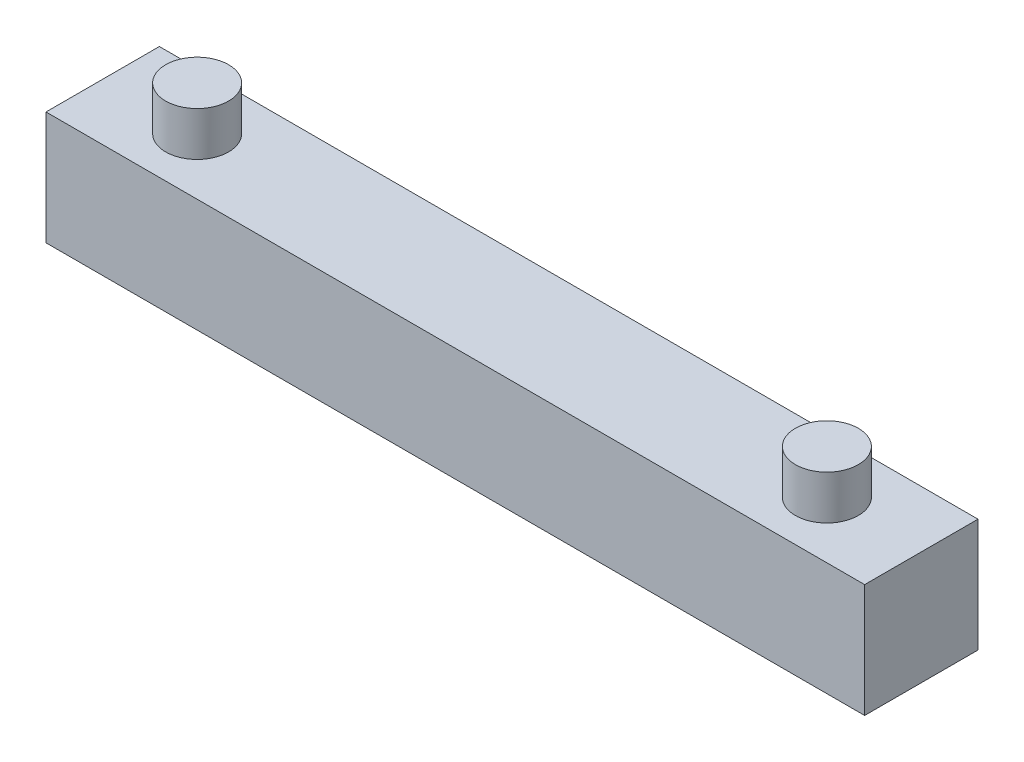
SolidWorks part; units mm, degrees
ref_plane "Front Plane" through (0, 0, 0) normal (0, 0, 1) x (1, 0, 0)
ref_plane "Top Plane" through (0, 0, 0) normal (0, 1, 0) x (1, 0, 0)
ref_plane "Right Plane" through (0, 0, 0) normal (1, 0, 0) x (0, 0, -1)
sketch "Sketch1" plane through (0, 0, 0) normal (0, 0, 1) x (1, 0, 0)
  line L1 (0, 0) -> (65, 0)
  line L2 (0, 0) -> (0, 9)
  line L3 (0, 9) -> (65, 9)
  line L4 (65, 0) -> (65, 9)
  dimension "D1" = 65
  dimension "D2" = 9
extrude "Boss-Extrude1" add sketch "Sketch1" along normal blind 9
sketch "Sketch2" plane through (0, 9, 0) normal (0, 1, 0) x (1, 0, 0)
  line L0 (0, -9) -> (0, 0) construction
  circle A0 centre (7.5, -4.5) radius 2.5
  circle A1 centre (57.5, -4.5) radius 2.5
  point P4 (0, -4.5)
  dimension "D1" = 5
  dimension "D4" = 4.5
  dimension "D2" = 50
  dimension "D3" = 7.5
extrude "Boss-Extrude2" add sketch "Sketch2" along normal blind 3.5
